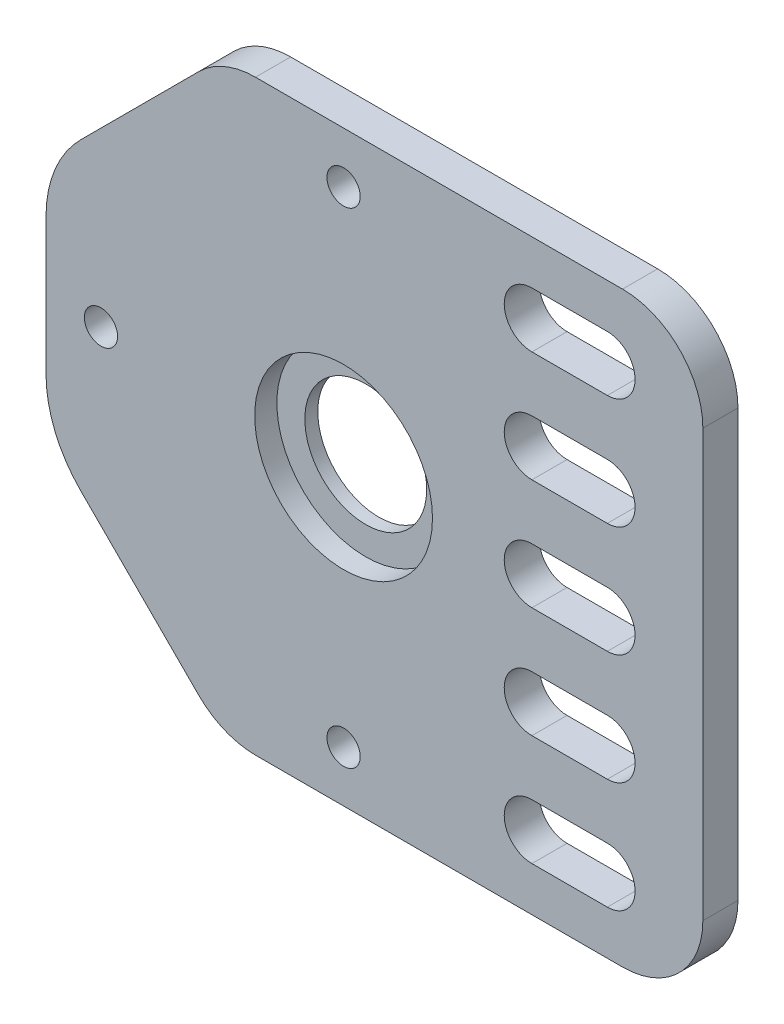
SolidWorks part; units mm, degrees
ref_plane "Front Plane" through (0, 0, 0) normal (0, 0, 1) x (1, 0, 0)
ref_plane "Top Plane" through (0, 0, 0) normal (0, 1, 0) x (1, 0, 0)
ref_plane "Right Plane" through (0, 0, 0) normal (1, 0, 0) x (0, 0, -1)
sketch "Sketch1" plane through (0, 0, 0) normal (0, 0, 1) x (1, 0, 0)
  line L0 (25.18, -26.5) -> (-7.947, -26.5)
  line L1 (-13.0735, -24.3765) -> (-23.7319, -13.7181)
  line L2 (-26.86, -6.1662) -> (-26.86, 6.1662)
  line L3 (-23.7319, 13.7181) -> (-13.0735, 24.3765)
  line L4 (-7.947, 26.5) -> (25.18, 26.5)
  line L5 (32.43, 19.25) -> (32.43, -19.25)
  line L6 (-26.86, 0) -> (0, 0) construction
  line L7 (0, 0) -> (32.43, 0) construction
  line L8 (-21.9, 0) -> (0, 21.9) construction
  line L9 (17, 0) -> (17, 20) construction
  line L10 (17, 20) -> (23.81, 20) construction
  line L11 (17, 22.5) -> (23.81, 22.5)
  line L12 (17, 17.5) -> (23.81, 17.5)
  line L13 (17, 10) -> (23.81, 10) construction
  line L14 (17, 12.5) -> (23.81, 12.5)
  line L15 (17, 7.5) -> (23.81, 7.5)
  line L16 (17, 0) -> (23.81, 0) construction
  line L17 (17, 2.5) -> (23.81, 2.5)
  line L18 (17, -2.5) -> (23.81, -2.5)
  line L19 (17, -10) -> (23.81, -10) construction
  line L20 (17, -7.5) -> (23.81, -7.5)
  line L21 (17, -12.5) -> (23.81, -12.5)
  line L22 (17, -20) -> (23.81, -20) construction
  line L23 (17, -17.5) -> (23.81, -17.5)
  line L24 (17, -22.5) -> (23.81, -22.5)
  line L25 (-21.9, 0) -> (0, -21.9) construction
  line L26 (0, -21.9) -> (-10.95, -10.95) construction
  line L27 (-10.95, -10.95) -> (-10.95, -26.5) construction
  circle A0 centre (0, 0) radius 5.5
  circle A1 centre (0, 21.9) radius 1.5
  circle A2 centre (-21.9, 0) radius 1.5
  circle A3 centre (0, -21.9) radius 1.5
  arc A4 (17, 22.5) -> (17, 17.5) centre (17, 20) ccw
  arc A5 (23.81, 17.5) -> (23.81, 22.5) centre (23.81, 20) ccw
  arc A6 (17, 12.5) -> (17, 7.5) centre (17, 10) ccw
  arc A7 (23.81, 7.5) -> (23.81, 12.5) centre (23.81, 10) ccw
  arc A8 (17, 2.5) -> (17, -2.5) centre (17, 0) ccw
  arc A9 (23.81, -2.5) -> (23.81, 2.5) centre (23.81, 0) ccw
  arc A10 (17, -7.5) -> (17, -12.5) centre (17, -10) ccw
  arc A11 (23.81, -12.5) -> (23.81, -7.5) centre (23.81, -10) ccw
  arc A12 (17, -17.5) -> (17, -22.5) centre (17, -20) ccw
  arc A13 (23.81, -22.5) -> (23.81, -17.5) centre (23.81, -20) ccw
  arc A14 (-23.7319, -13.7181) -> (-26.86, -6.1662) centre (-16.18, -6.1662) cw
  arc A15 (-26.86, 6.1662) -> (-23.7319, 13.7181) centre (-16.18, 6.1662) cw
  arc A16 (-7.947, -26.5) -> (-13.0735, -24.3765) centre (-7.947, -19.25) cw
  arc A17 (25.18, -26.5) -> (32.43, -19.25) centre (25.18, -19.25) ccw
  arc A18 (25.18, 26.5) -> (32.43, 19.25) centre (25.18, 19.25) cw
  arc A19 (-13.0735, 24.3765) -> (-7.947, 26.5) centre (-7.947, 19.25) cw
  point P14 (20.405, 20)
  point P26 (20.405, 10)
  point P33 (20.405, 0)
  point P40 (20.405, -10)
  point P47 (20.405, -20)
  dimension "D1" = 11
  dimension "D5" = 3
  dimension "D11" = 10.68
  dimension "D12" = 7.25
  dimension "D2" = 59.29
  dimension "D3" = 45
  dimension "D4" = 26.86
  dimension "D6" = 21.9
  dimension "D7" = 20
  dimension "D8" = 43.86
  dimension "D9" = 6.81
  dimension "D10" = 5
extrude "Boss-Extrude1" add sketch "Sketch1" along normal mid plane 3.17
sketch "Sketch3" plane through (0, 0, 1.585) normal (0, 0, 1) x (1, 0, 0)
  circle A0 centre (0, 0) radius 8.025
  dimension "D1" = 16.05
extrude "Cut-Extrude1" cut sketch "Sketch3" against normal blind 2
